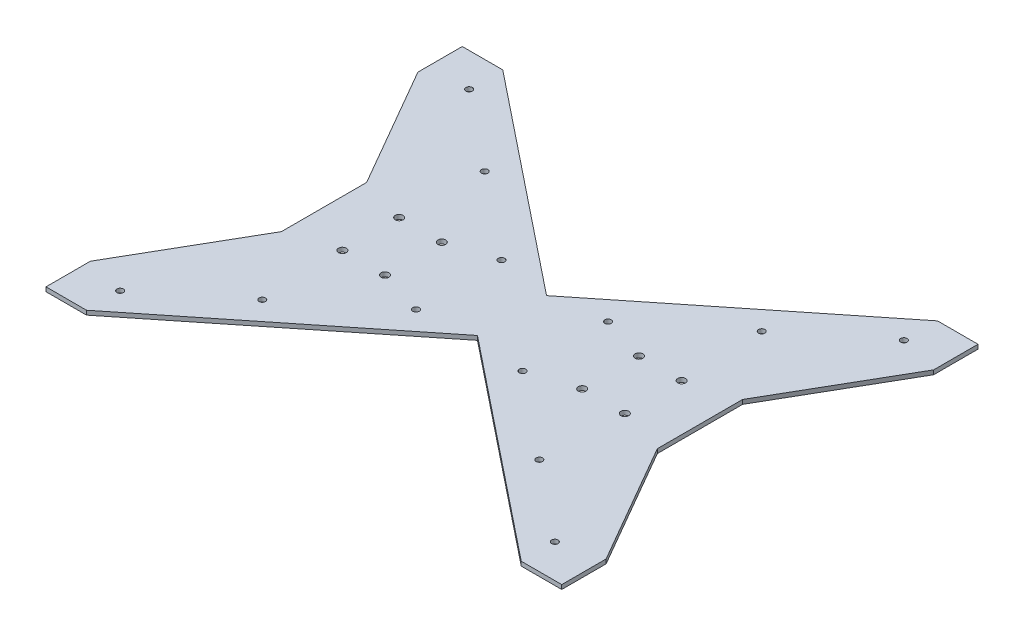
SolidWorks part; units mm, degrees
ref_plane "Front Plane" through (0, 0, 0) normal (0, 0, 1) x (1, 0, 0)
ref_plane "Top Plane" through (0, 0, 0) normal (0, 1, 0) x (1, 0, 0)
ref_plane "Right Plane" through (0, 0, 0) normal (1, 0, 0) x (0, 0, -1)
sketch "Sketch1" plane through (0, 0, 0) normal (0, 1, 0) x (1, 0, 0)
  line L1 (-182.5, -146.5) -> (182.5, -146.5)
  line L2 (-182.5, -146.5) -> (-182.5, 146.5)
  line L3 (-182.5, 146.5) -> (182.5, 146.5)
  line L4 (182.5, -146.5) -> (182.5, 146.5)
  line L5 (-182.5, -146.5) -> (182.5, 146.5) construction
  line L6 (-182.5, 146.5) -> (182.5, -146.5) construction
  point P0 (0, 0)
  dimension "D1" = 293
  dimension "D2" = 365
extrude "Boss-Extrude1" add sketch "Sketch1" along normal blind 3
sketch "Sketch2" plane through (0, 3, 0) normal (0, 1, 0) x (1, 0, 0)
  line L0 (-182.5, 146.5) -> (182.5, -146.5) construction
  line L1 (182.5, 146.5) -> (-182.5, -146.5) construction
sketch "Sketch3" plane through (0, 3, 0) normal (0, 1, 0) x (1, 0, 0)
  line L0 (-153, 146.5) -> (0, 24.3)
  line L1 (182.5, 146.5) -> (-182.5, 146.5) construction
  line L2 (-153, 146.5) -> (153, 146.5)
  line L3 (153, 146.5) -> (0, 24.3)
  dimension "D1" = 29.5
  dimension "D2" = 29.5
  dimension "D3" = 24.3
extrude "Cut-Extrude1" cut sketch "Sketch3" against normal through all
ref_plane "Plane2" through (0, 0, 0) normal (0, 0, 1) x (1, 0, 0)
mirror "Mirror3" about plane through (0, 0, 0) normal (0, 0, 1) of "Cut-Extrude1"
sketch "Sketch5" plane through (0, 3, 0) normal (0, 1, 0) x (1, 0, 0)
  line L0 (-132.3077, 30) -> (-182.5, 117)
  line L1 (-182.5, 146.5) -> (-182.5, -146.5) construction
  line L2 (-132.3077, -30) -> (-182.5, -117)
  line L3 (-182.5, 117) -> (-182.5, -117)
  line L4 (-132.3077, 30) -> (-132.3077, -30)
  dimension "D1" = 29.5
  dimension "D2" = 29.5
  dimension "D4" = 60
extrude "Cut-Extrude2" cut sketch "Sketch5" against normal through all
ref_plane "Plane4" through (0, 0, 0) normal (1, 0, 0) x (0, 1, 0)
mirror "Mirror4" about plane through (0, 0, 0) normal (1, 0, 0) of "Cut-Extrude2"
sketch "Sketch8" plane through (0, 3, 0) normal (0, 1, 0) x (1, 0, 0)
  line L0 (-132.3077, -30) -> (-132.3077, 30) construction
  circle A0 centre (-99.4077, 20) radius 2.75
  circle A1 centre (-69.4077, 20) radius 2.75
  dimension "D3" = 5.5
  dimension "D5" = 5.5
  dimension "D4" = 30
  dimension "D1" = 32.9
  dimension "D2" = 10
extrude "Cut-Extrude3" cut sketch "Sketch8" against normal through all
mirror "Mirror5" about plane through (0, 0, 0) normal (0, 0, 1) of "Cut-Extrude3"
mirror "Mirror6" about plane through (0, 0, 0) normal (1, 0, 0) of "Mirror5", "Cut-Extrude3"
sketch "Sketch9" plane through (0, 3, 0) normal (0, 1, 0) x (1, 0, 0)
  line L0 (182.5, 146.5) -> (-182.5, -146.5) construction
  line L3 (182.5, 117) -> (182.5, 146.5) construction
  circle A0 centre (153, 122.8192) radius 2.25
  circle A1 centre (37.5, 30.1027) radius 2.25
  circle A2 centre (97.5, 78.2671) radius 2.25
  dimension "D1" = 4.5
  dimension "D2" = 4.5
  dimension "D3" = 4.5
  dimension "D5" = 145
  dimension "D4" = 85
extrude "Cut-Extrude4" cut sketch "Sketch9" against normal through all
mirror "Mirror7" about plane through (0, 0, 0) normal (1, 0, 0) of "Cut-Extrude4"
mirror "Mirror8" about plane through (0, 0, 0) normal (0, 0, 1) of "Mirror7", "Cut-Extrude4"
sketch "Sketch10" plane through (0, 3, 0) normal (0, 1, 0) x (1, 0, 0)
  line L0 (-182.5, -146.5) -> (-153, -146.5) construction
  line L1 (-182.5, 146.5) -> (-181.5, 146.5)
  line L2 (-182.5, 146.5) -> (-182.5, -146.5)
  line L3 (-182.5, -146.5) -> (-181.5, -146.5)
  line L4 (-181.5, 146.5) -> (-181.5, -146.5)
  line L5 (153, -146.5) -> (182.5, -146.5) construction
  line L6 (182.5, 146.5) -> (181.5, 146.5)
  line L7 (182.5, 146.5) -> (182.5, -146.5)
  line L8 (182.5, -146.5) -> (181.5, -146.5)
  line L9 (181.5, 146.5) -> (181.5, -146.5)
  dimension "D1" = 1
  dimension "D2" = 1
extrude "Cut-Extrude5" cut sketch "Sketch10" against normal through all
